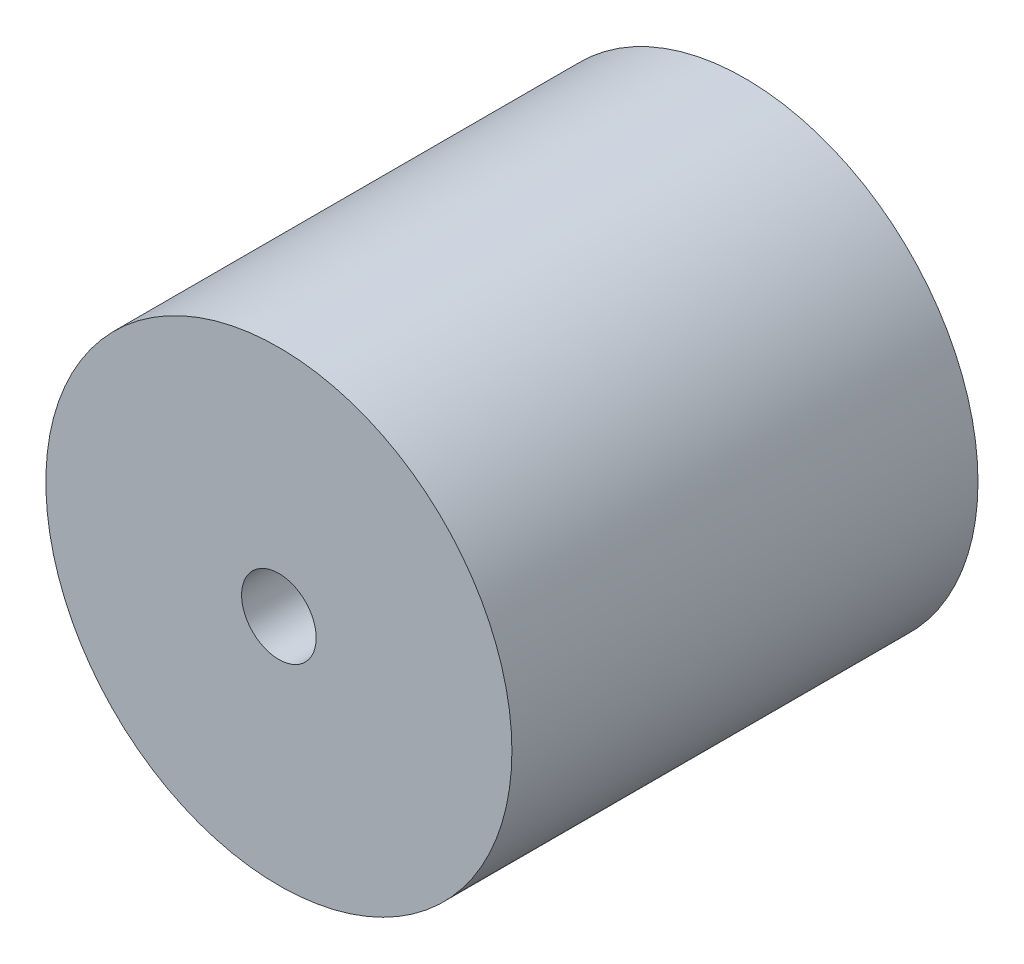
SolidWorks part; units mm, degrees
material "ABS"
ref_plane "Front Plane" through (0, 0, 0) normal (0, 0, 1) x (1, 0, 0)
ref_plane "Top Plane" through (0, 0, 0) normal (0, 1, 0) x (1, 0, 0)
ref_plane "Right Plane" through (0, 0, 0) normal (1, 0, 0) x (0, 0, -1)
sketch "Sketch1" plane through (0, 0, 0) normal (0, 0, 1) x (1, 0, 0)
  circle A0 centre (0, 0) radius 12.5
  circle A1 centre (0, 0) radius 2
  dimension "D1" = 25
  dimension "D2" = 4
extrude "Boss-Extrude1" add sketch "Sketch1" along normal blind 25
